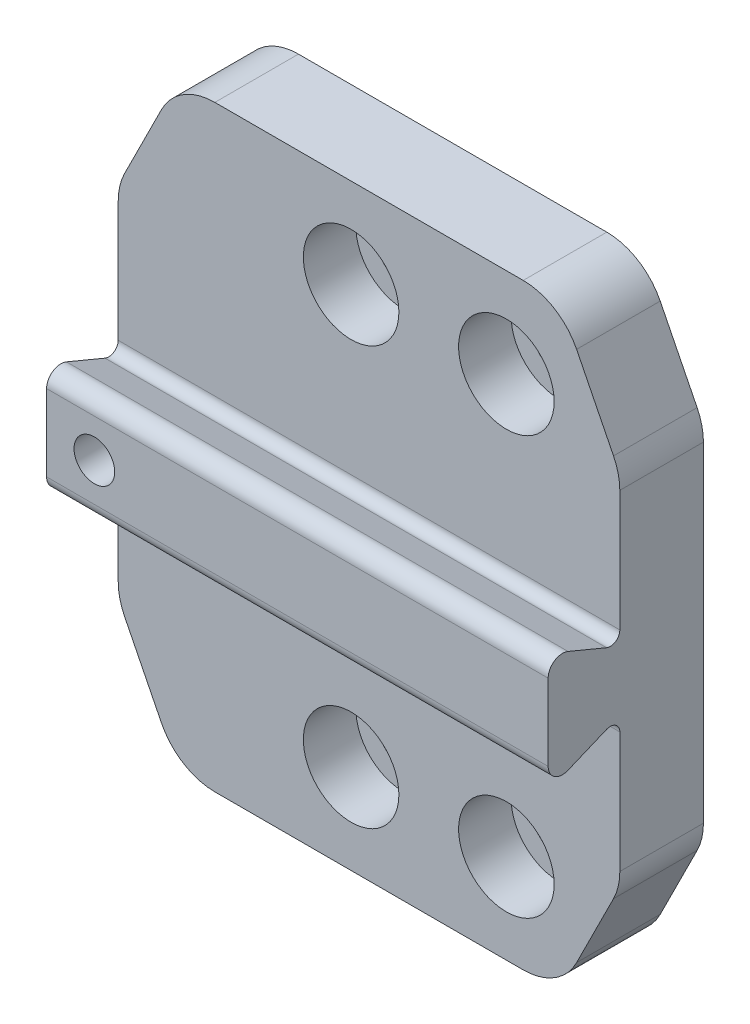
SolidWorks part; units mm, degrees
material "PUR"
ref_plane "Ebene vorne" through (0, 0, 0) normal (0, 0, 1) x (1, 0, 0)
ref_plane "Ebene oben" through (0, 0, 0) normal (0, 1, 0) x (1, 0, 0)
ref_plane "Ebene rechts" through (0, 0, 0) normal (1, 0, 0) x (0, 0, -1)
sketch "Skizze1" plane through (0, 0, 0) normal (0, 0, 1) x (1, 0, 0)
  line L1 (21, -25) -> (-21, -25)
  line L2 (21, -25) -> (21, 25)
  line L3 (21, 25) -> (-21, 25)
  line L4 (-21, -25) -> (-21, 25)
  line L5 (21, -25) -> (-21, 25) construction
  line L6 (21, 25) -> (-21, -25) construction
  point P0 (0, 0)
  dimension "D1" = 50
  dimension "D2" = 42
extrude "Aufsatz-Linear austragen1" add sketch "Skizze1" along normal blind 7
hole_wizard "Stirnsenkung für M4 Zylinderschraube mit Innensechskant1" positions "Skizze2" profile "Skizze3" counterbore size "M4" standard "ISO" end condition through all
sketch "Skizze2" plane through (0, 0, 7) normal (0, 0, 1) x (1, 0, 0)
  line L0 (-1.5, -17.5) -> (-1.5, 17.5) construction
  line L1 (-1.5, 17.5) -> (11.5, 17.5) construction
  line L2 (11.5, 17.5) -> (11.5, -17.5) construction
  line L3 (11.5, -17.5) -> (-1.5, -17.5) construction
  line L6 (21, -25) -> (21, 25) construction
  point P0 (-1.5, 17.5)
  point P2 (11.5, 17.5)
  point P4 (11.5, -17.5)
  point P6 (-1.5, -17.5)
  point P17 (11.5, 0)
  dimension "D1" = 13
  dimension "D2" = 35
  dimension "D3" = 9.5
sketch "Skizze3" plane through (-1.5, 17.5, 7) normal (1, 0, 0) x (0, -1, 0)
  line L0 (0, 0) -> (0, 7)
  line L1 (0, 7) -> (2.25, 7)
  line L3 (2.25, 7) -> (2.25, 4.4)
  line L4 (2.25, 4.4) -> (4, 4.4)
  line L5 (4, 4.4) -> (4, 0)
  line L7 (4, 0) -> (0, 0)
  line L11 (0, -6.35) -> (0, 107.95) construction
  dimension "Bohrerdurchmesser" = 4.5
  dimension "Bohrungstiefe" = 7
  dimension "Senkdurchmesser2" = 8
  dimension "Senktiefe2" = 4.4
sketch "Skizze4" plane through (21, 0, 0) normal (1, 0, 0) x (0, 0, -1)
  line L0 (-7, 2.5) -> (-13, 5)
  line L1 (-7, -25) -> (-7, 25) construction
  line L2 (-13, 5) -> (-13, -5)
  line L3 (-13, -5) -> (-7, -2.5)
  line L4 (-7, -2.5) -> (-7, 2.5)
  point P7 (-7, 0)
  dimension "D1" = 10
  dimension "D2" = 5
  dimension "D3" = 6
extrude "Aufsatz-Linear austragen2" add sketch "Skizze4" against normal through all
fillet "Verrundung1" radius 0.8 2 edges at (0, 2.5, 7) (0, -2.5, 7)
sketch "Skizze5" plane through (0, 0, 0) normal (0, 0, -1) x (-1, 0, 0)
  line L0 (-21, 25) -> (-21, 15)
  line L1 (-21, -25) -> (-21, 25) construction
  line L2 (-21, 15) -> (-16, 25)
  line L3 (-21, 25) -> (21, 25) construction
  line L4 (-16, 25) -> (-21, 25)
  line L5 (21, 25) -> (16, 25)
  line L6 (16, 25) -> (21, 15)
  line L7 (21, 25) -> (21, -25) construction
  line L8 (21, 15) -> (21, 25)
  line L9 (-21, -15) -> (-21, -25)
  line L10 (-21, -25) -> (-16, -25)
  line L11 (21, -25) -> (-21, -25) construction
  line L12 (-16, -25) -> (-21, -15)
  line L13 (16, -25) -> (21, -25)
  line L14 (21, -25) -> (21, -15)
  line L15 (21, -15) -> (16, -25)
  dimension "D1" = 32
  dimension "D2" = 30
extrude "Schnitt-Linear austragen1" cut sketch "Skizze5" against normal through all
fillet "Verrundung2" radius 5 8 edges at (-21, -15, 3.5) (-16, -25, 3.5) (16, -25, 3.5) (-16, 25, 3.5) (-21, 15, 3.5) (21, -15, 3.5) (21, 15, 3.5) (16, 25, 3.5)
fillet "Verrundung3" radius 1.2 2 edges at (0, -5, 13) (0, 5, 13)
hole_wizard "Stirnsenkung für M3 Zylinderschraube mit Innensechskant1" positions "Skizze6" profile "Skizze7" counterbore size "M3" standard "ISO" end condition through all
sketch "Skizze6" plane through (0, 0, 0) normal (0, 0, -1) x (-1, 0, 0)
  line L0 (17, 0) -> (0, 0) construction
  line L2 (21, 13.8197) -> (21, -13.8197) construction
  point P0 (17, 0)
  dimension "D1" = 4
sketch "Skizze7" plane through (-17, 0, 0) normal (1, 0, 0) x (0, 1, 0)
  line L0 (0, 0) -> (0, 13)
  line L1 (0, 13) -> (1.7, 13)
  line L3 (1.7, 13) -> (1.7, 3.4)
  line L4 (1.7, 3.4) -> (3.25, 3.4)
  line L5 (3.25, 3.4) -> (3.25, 0)
  line L7 (3.25, 0) -> (0, 0)
  line L11 (0, -6.35) -> (0, 107.95) construction
  dimension "Bohrerdurchmesser" = 3.4
  dimension "Bohrungstiefe" = 13
  dimension "Senkdurchmesser2" = 6.5
  dimension "Senktiefe2" = 3.4
